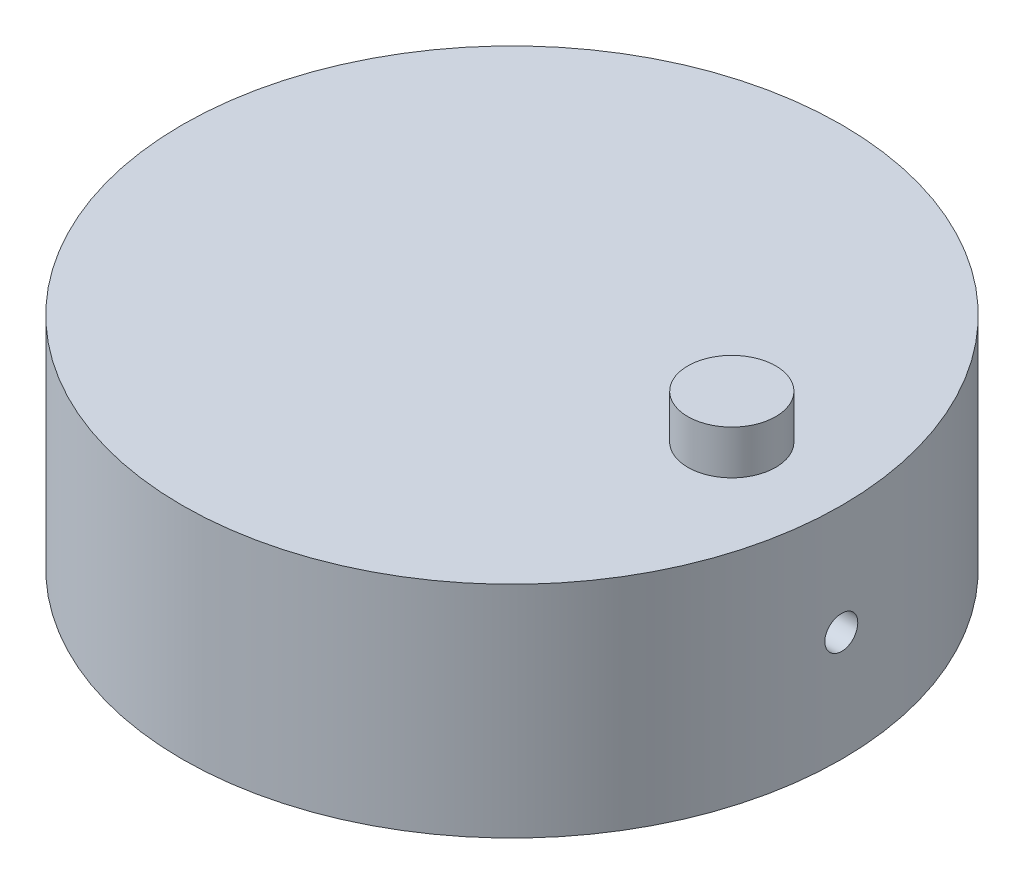
SolidWorks part; units mm, degrees
ref_plane "Front Plane" through (0, 0, 0) normal (0, 0, 1) x (1, 0, 0)
ref_plane "Top Plane" through (0, 0, 0) normal (0, 1, 0) x (1, 0, 0)
ref_plane "Right Plane" through (0, 0, 0) normal (1, 0, 0) x (0, 0, -1)
sketch "Sketch1" plane through (0, 0, 0) normal (0, 1, 0) x (1, 0, 0)
  circle A0 centre (0, 0) radius 38.1
  dimension "D1" = 76.2
extrude "Boss-Extrude1" add sketch "Sketch1" along normal blind 25.4
sketch "Sketch2" plane through (0, 25.4, 0) normal (0, 1, 0) x (1, 0, 0)
  circle A0 centre (25.4, 0) radius 5.08
  dimension "D1" = 10.16
  dimension "D2" = 25.4
extrude "Boss-Extrude2" add sketch "Sketch2" along normal blind 5.08
sketch "Sketch3" plane through (0, 0, 0) normal (1, 0, 0) x (0, 0, -1)
  circle A0 centre (0, 12.7) radius 1.905
  dimension "D1" = 3.81
extrude "Cut-Extrude1" cut sketch "Sketch3" against normal blind 46.482 and the other way blind 46.228
